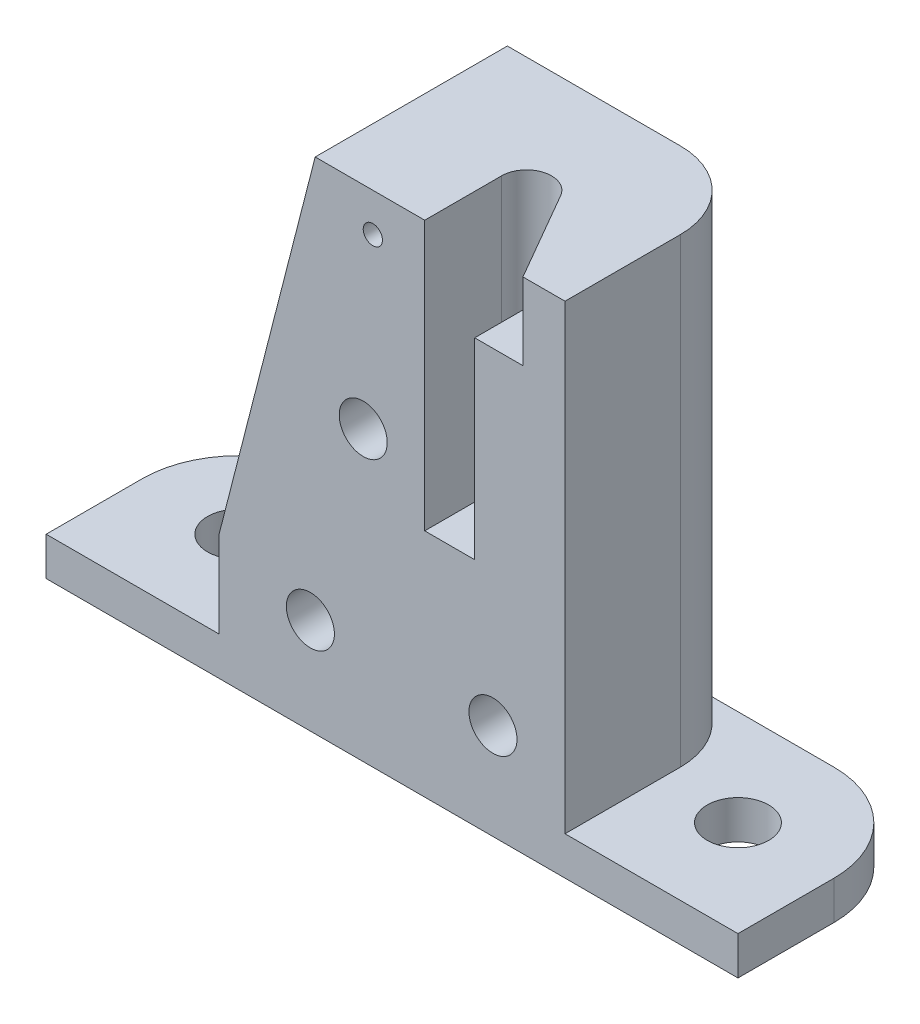
SolidWorks part; units mm, degrees
material "ABS"
ref_plane "Front Plane" through (0, 0, 0) normal (0, 0, 1) x (1, 0, 0)
ref_plane "Top Plane" through (0, 0, 0) normal (0, 1, 0) x (1, 0, 0)
ref_plane "Right Plane" through (0, 0, 0) normal (1, 0, 0) x (0, 0, -1)
sketch "Sketch1" plane through (0, 0, 0) normal (0, 1, 0) x (1, 0, 0)
  line L0 (0, 0) -> (36, 0)
  line L1 (9, 10) -> (5, 10)
  line L2 (9, 10) -> (27, 10)
  line L3 (27, 10) -> (31, 10)
  line L4 (0, 0) -> (0, 5)
  line L5 (36, 0) -> (36, 5)
  arc A0 (5, 10) -> (0, 5) centre (5, 5) ccw
  arc A1 (31, 10) -> (36, 5) centre (31, 5) cw
  circle A2 centre (5, 5) radius 1.6
  circle A3 centre (31, 5) radius 1.6
  dimension "D1" = 18
  dimension "D2" = 36
  dimension "D5" = 3.2
  dimension "D4" = 5
  dimension "D3" = 10
extrude "Boss-Extrude1" add sketch "Sketch1" along normal blind 2
sketch "Sketch2" plane through (0, 0, 0) normal (0, 1, 0) x (1, 0, 0)
  line L0 (27, 0) -> (27, 6)
  line L2 (23, 10) -> (13, 10)
  line L4 (9, 6) -> (9, 0)
  line L5 (9, 0) -> (27, 0)
  line L6 (0, 0) -> (36, 0) construction
  line L7 (9, 0) -> (0, 0) construction
  line L8 (27, 0) -> (36, 0) construction
  line L9 (36, 0) -> (36, 5) construction
  arc A0 (27, 6) -> (23, 10) centre (23, 6) ccw
  arc A1 (13, 10) -> (9, 6) centre (13, 6) ccw
  dimension "D2" = 4
  dimension "D1" = 10
  dimension "D3" = 18
extrude "Boss-Extrude2" add sketch "Sketch2" along normal blind 26
sketch "Sketch3" plane through (0, 26, 0) normal (0, 1, 0) x (1, 0, 0)
  line L0 (9, 0) -> (27, 0) construction
  line L1 (27, 0) -> (27, 6) construction
  circle A0 centre (21, 4) radius 1.2
  dimension "D1" = 2.4
  dimension "D2" = 4
  dimension "D3" = 6
extrude "Cut-Extrude1" cut sketch "Sketch3" against normal up to next
sketch "Sketch4" plane through (0, 26, 0) normal (0, 1, 0) x (1, 0, 0)
  line L0 (22.1258, 4.65) -> (24.8105, 0)
  line L1 (9, 0) -> (27, 0) construction
  line L2 (24.8105, 0) -> (19.7, 0)
  line L3 (19.7, 0) -> (19.7, 4)
  arc A1 (19.7, 4) -> (22.1258, 4.65) centre (21, 4) cw
  circle A2 centre (21, 4) radius 1.2 construction
  dimension "D2" = 1.3
  dimension "D1" = 120
extrude "Cut-Extrude2" cut sketch "Sketch4" against normal blind 4
sketch "Sketch5" plane through (0, 26, 0) normal (0, 1, 0) x (1, 0, 0)
  line L0 (19.7, 4) -> (19.7, 0)
  line L1 (19.7, 4) -> (19.7, 0) construction
  line L6 (19.7, 4) -> (19.7, 0) construction
  line L7 (22.3, 4) -> (22.3, 0)
  line L9 (19.7, 0) -> (22.3, 0)
  line L10 (9, 0) -> (0, 0) construction
  arc A0 (19.7, 4) -> (22.3, 4) centre (21, 4) cw
  arc A3 (22.1258, 4.65) -> (19.7, 4) centre (21, 4) ccw construction
extrude "Cut-Extrude3" cut sketch "Sketch5" against normal blind 14
sketch "Sketch6" plane through (0, 0, 0) normal (0, 0, 1) x (1, 0, 0)
  line L0 (9, 26) -> (19.7, 26) construction
  line L3 (0, 0) -> (36, 0) construction
  line L4 (9, 6.5) -> (14, 26)
  line L6 (14, 26) -> (9, 26)
  line L7 (9, 26) -> (9, 6.5)
  line L9 (9, 26) -> (9, 2) construction
  line L10 (0, 0) -> (36, 0) construction
  line L11 (27, 26) -> (27, 2) construction
  circle A0 centre (17, 24) radius 0.5
  circle A1 centre (16.5, 15) radius 1.25
  circle A2 centre (13.75, 5) radius 1.25
  circle A3 centre (23.25, 5) radius 1.25
  dimension "D1" = 1
  dimension "D2" = 2
  dimension "D3" = 10
  dimension "D4" = 2.5
  dimension "D5" = 11
  dimension "D6" = 10.5
  dimension "D7" = 9.5
  dimension "D8" = 5
  dimension "D9" = 3.75
  dimension "D10" = 6.5
  dimension "D11" = 13
extrude "Cut-Extrude4" cut sketch "Sketch6" against normal up to next
